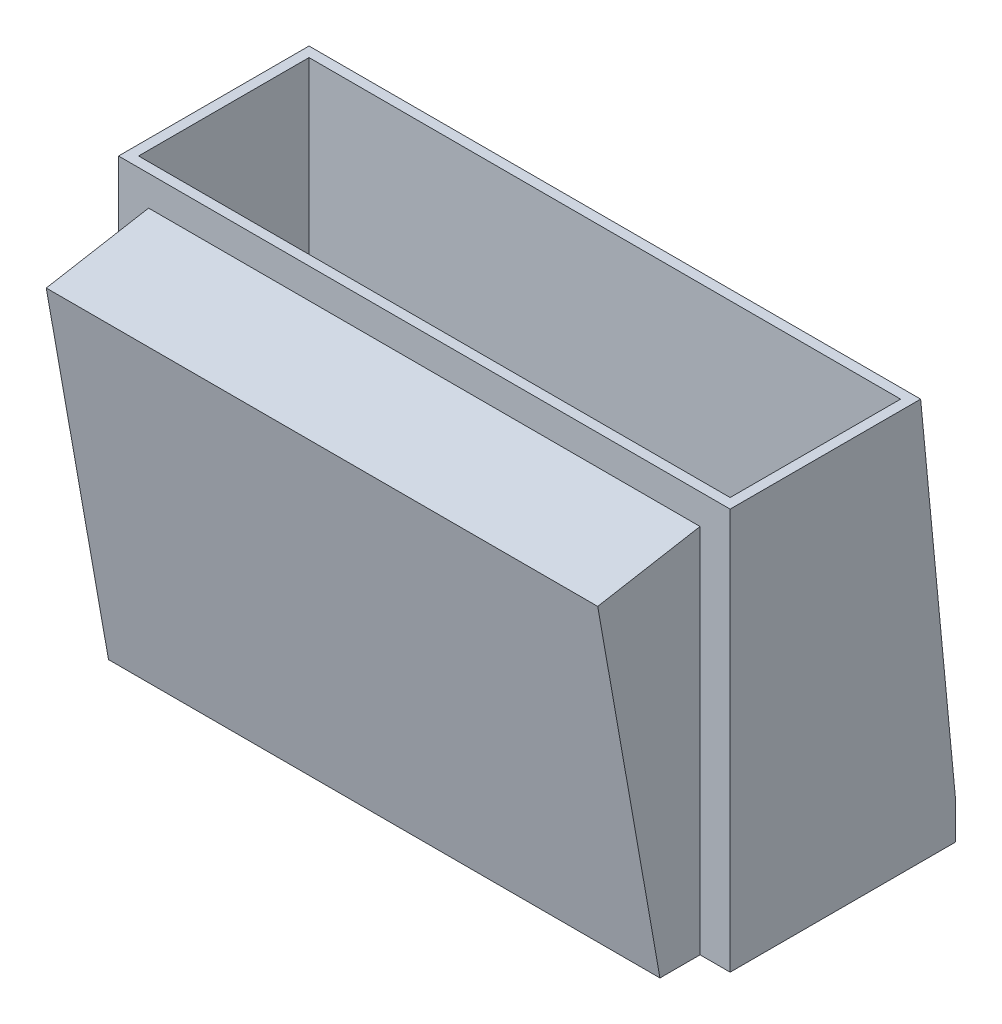
SolidWorks part; units mm, degrees
ref_plane "Front Plane" through (0, 0, 0) normal (0, 0, 1) x (1, 0, 0)
ref_plane "Top Plane" through (0, 0, 0) normal (0, 1, 0) x (1, 0, 0)
ref_plane "Right Plane" through (0, 0, 0) normal (1, 0, 0) x (0, 0, -1)
sketch "Sketch1" plane through (0, 0, 0) normal (0, 1, 0) x (1, 0, 0)
  line L0 (-14.75, 4.25) -> (-15.25, 4.25) construction
  line L1 (-14.75, 4.25) -> (14.75, 4.25)
  line L2 (-14.75, 4.25) -> (-14.75, -4.25)
  line L3 (-14.75, -4.25) -> (14.75, -4.25)
  line L4 (14.75, 4.25) -> (14.75, -4.25)
  line L5 (-14.75, 4.25) -> (14.75, -4.25) construction
  line L6 (-14.75, -4.25) -> (14.75, 4.25) construction
  line L7 (15.25, 4.75) -> (-15.25, 4.75)
  line L8 (15.25, 4.75) -> (15.25, -4.75)
  line L9 (15.25, -4.75) -> (-15.25, -4.75)
  line L10 (-15.25, 4.75) -> (-15.25, -4.75)
  line L11 (15.25, 4.75) -> (-15.25, -4.75) construction
  line L12 (15.25, -4.75) -> (-15.25, 4.75) construction
  line L13 (-14.75, 4.25) -> (-14.75, 4.75) construction
  line L17 (-15.25, -4.75) -> (15.25, -4.75)
  point P0 (0, 0)
  point P6 (0, 0)
  dimension "D1" = 29.5
  dimension "D2" = 8.5
  dimension "D3" = 0.5
extrude "Boss-Extrude1" add sketch "Sketch1" along normal blind 20
sketch "Sketch2" plane through (-15.25, 0, 0) normal (-1, 0, 0) x (0, 0, 1)
  line L0 (4.75, 0) -> (6.75, 0)
  line L1 (6.75, 0) -> (9.8534, 17.6001)
  line L2 (9.8534, 17.6001) -> (4.75, 18.5)
  line L3 (6.75, 0) -> (6.75, 18.1473) construction
  line L4 (4.75, 18.5) -> (4.75, 0)
  line L5 (-4.75, 0) -> (-6.5, 0)
  line L6 (-6.5, 0) -> (-6.5, 1.75)
  line L7 (-6.5, 1.75) -> (-4.75, 20)
  line L8 (-4.75, 20) -> (4.75, 20) construction
  point P10 (0, 0)
  line M6 (4.75, 0) -> (4.75, 20)
  line M8 (-4.75, 20) -> (-4.75, 0)
  dimension "D1" = 10
  dimension "D2" = 2
  dimension "D3" = 1.75
  dimension "D4" = 1.5
extrude "Boss-Extrude2" add sketch "Sketch2" against normal up to surface (30.5 mm away) contours L3 L1 L2 | L0 L3 L2 M6 | L7 L6 L5 M8 up to face at (15.25, 10, 0)
sketch "Sketch3" plane through (-15.25, 0, 0) normal (-1, 0, 0) x (0, 0, 1)
  line L0 (9.8534, 17.6001) -> (4.75, 18.5) construction
  line L2 (4.75, 18.5) -> (9.8534, 17.6001)
  line L3 (9.8534, 17.6001) -> (6.75, 0)
  line L4 (6.75, 0) -> (4.75, 0)
  line L5 (4.75, 0) -> (4.75, 18.5)
  dimension "D1" = 0.5
extrude "Cut-Extrude1" cut sketch "Sketch3" against normal blind 1.5
ref_plane "Plane1" through (0, 0, 0) normal (-1, 0, 0) x (0, 0, 1)
mirror "Mirror1" about plane through (0, 0, 0) normal (-1, 0, 0) of "Cut-Extrude1"
